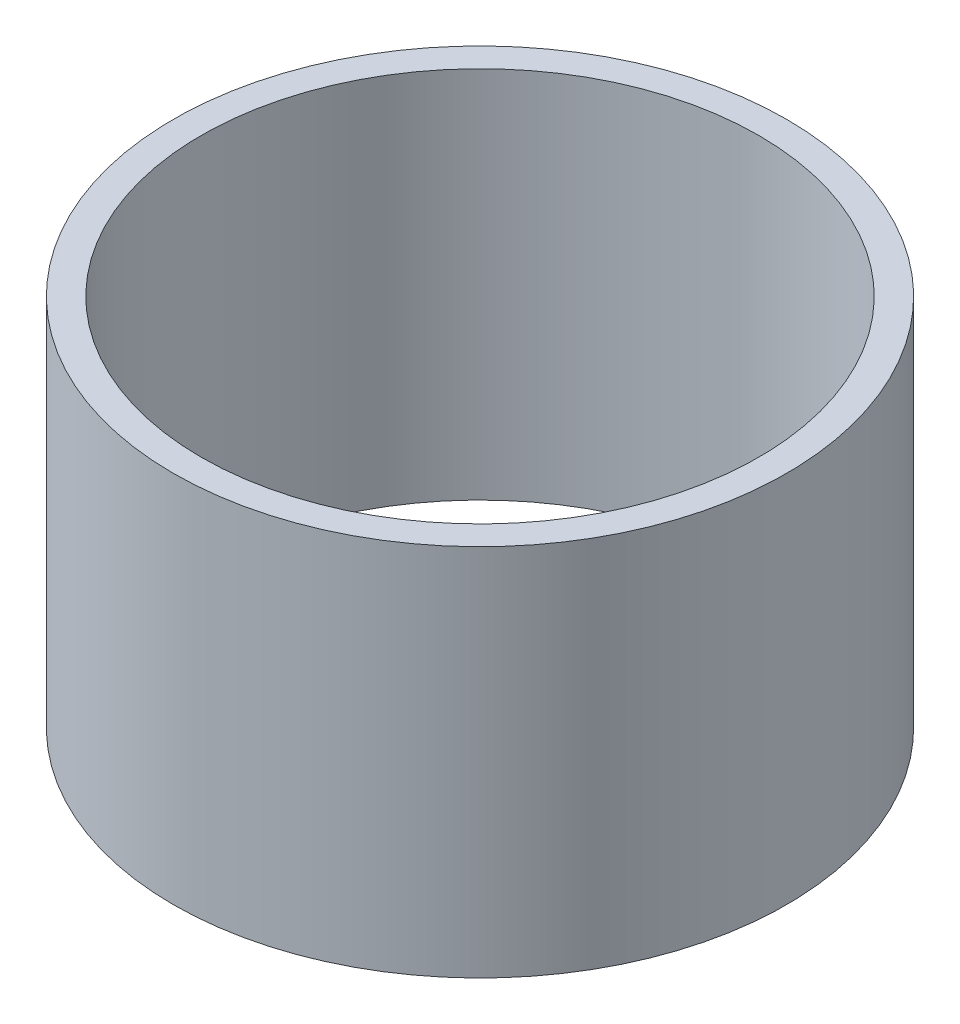
SolidWorks part; units mm, degrees
ref_plane "Front Plane" through (0, 0, 0) normal (0, 0, 1) x (1, 0, 0)
ref_plane "Top Plane" through (0, 0, 0) normal (0, 1, 0) x (1, 0, 0)
ref_plane "Right Plane" through (0, 0, 0) normal (1, 0, 0) x (0, 0, -1)
sketch "Sketch1" plane through (0, 0, 0) normal (0, 1, 0) x (1, 0, 0)
  circle A0 centre (0, 0) radius 50
  circle A1 centre (0, 0) radius 55
  dimension "D1" = 100
  dimension "D2" = 5
extrude "Boss-Extrude1" add sketch "Sketch1" along normal blind 67
